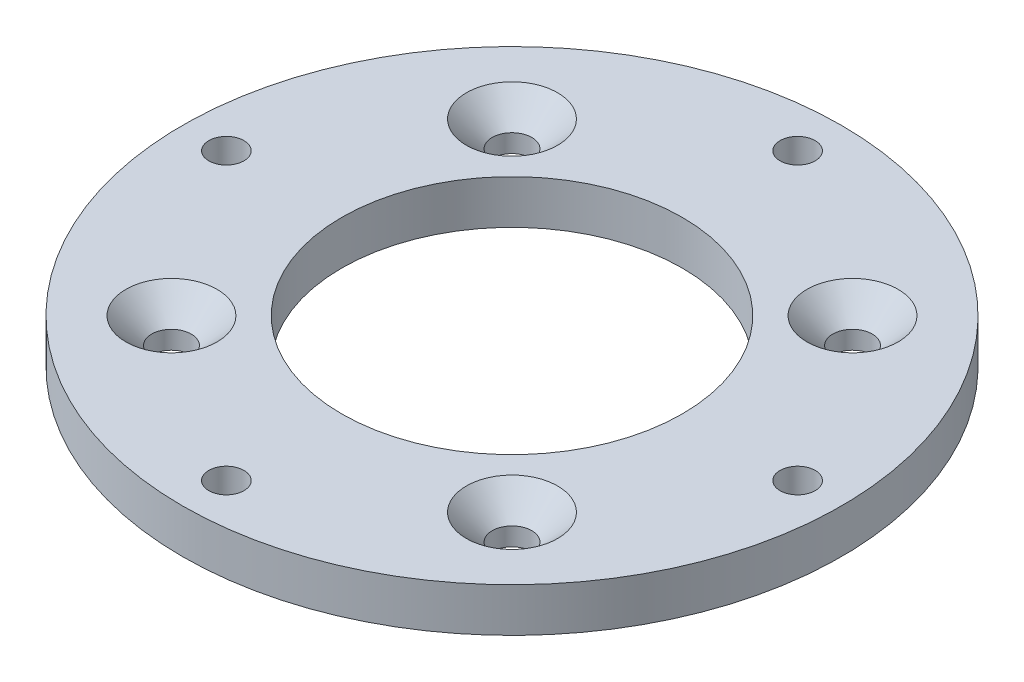
SolidWorks part; units mm, degrees
material "Acrylic (Medium-high impact)"
ref_plane "Front Plane" through (0, 0, 0) normal (0, 0, 1) x (1, 0, 0)
ref_plane "Top Plane" through (0, 0, 0) normal (0, 1, 0) x (1, 0, 0)
ref_plane "Right Plane" through (0, 0, 0) normal (1, 0, 0) x (0, 0, -1)
sketch "Sketch1" plane through (0, 0, 0) normal (0, 1, 0) x (1, 0, 0)
  circle A0 centre (0, 0) radius 30
  dimension "D1" = 60
extrude "Boss-Extrude1" add sketch "Sketch1" against normal blind 4
sketch "Sketch8" plane through (0, -4, 0) normal (0, -1, 0) x (1, 0, 0)
  line L1 (-15.5, -15.5) -> (15.5, -15.5) construction
  line L2 (-15.5, -15.5) -> (-15.5, 15.5) construction
  line L3 (-15.5, 15.5) -> (15.5, 15.5) construction
  line L4 (15.5, -15.5) -> (15.5, 15.5) construction
  line L5 (-15.5, -15.5) -> (15.5, 15.5) construction
  line L6 (-15.5, 15.5) -> (15.5, -15.5) construction
  circle A0 centre (0, 0) radius 15.5
  point P8 (0, 0)
  point P9 (0, 0)
  point P10 (0, 0)
  dimension "D1" = 31
extrude "Cut-Extrude1" cut sketch "Sketch8" against normal blind 6
sketch "Sketch14" plane through (0, 0, 0) normal (0, 1, 0) x (1, 0, 0)
  line L16 (-15.5, -15.5) -> (15.5, -15.5) construction
  line L17 (-15.5, -15.5) -> (-15.5, 15.5) construction
  line L18 (-15.5, 15.5) -> (15.5, 15.5) construction
  line L19 (15.5, -15.5) -> (15.5, 15.5) construction
  line L20 (-15.5, -15.5) -> (15.5, 15.5) construction
  line L21 (-15.5, 15.5) -> (15.5, -15.5) construction
  point P1889 (15.5, 15.5)
  point P1896 (-15.5, 15.5)
  point P1899 (-15.5, -15.5)
  point P1902 (15.5, -15.5)
  point P1903 (0, 0)
  dimension "D1" = 31
hole_wizard "CSK for M3 Countersunk Flat Head Screw2" positions "Sketch14" profile "Sketch16" countersink size "M3" standard "ISO" end condition through all
sketch "Sketch16" plane through (15.5, 0, 15.5) normal (1, 0, 0) x (0, 0, 1)
  line L0 (0, 0) -> (0, 4)
  line L1 (0, 4) -> (1.8, 4)
  line L2 (1.8, 4) -> (1.8, 2.35)
  line L3 (1.8, 2.35) -> (4.15, 0)
  line L5 (4.15, 0) -> (0, 0)
  line L6 (-1.8, 2.35) -> (-4.15, 0) construction
  line L11 (0, -6.35) -> (0, 107.95) construction
  dimension "Thru Hole Dia." = 3.6
  dimension "Thru Hole Depth" = 4
  dimension "Near C'Sink Dia." = 8.3
  dimension "Near C'Sink Angle" = 90
sketch "Sketch18" plane through (0, -4, 0) normal (0, -1, 0) x (1, 0, 0)
  point P0 (0, 26)
  point P5 (26, 0)
  point P6 (0, -26)
  point P7 (-26, 0)
  point P18 (0, 0)
  point P19 (0, 0)
  point P20 (0, 0)
  point P21 (0, 0)
  point P22 (0, 0)
  point P23 (0, 0)
  dimension "D1" = 26
  dimension "D2" = 4
hole_wizard "CSK for M3 Countersunk Flat Head Screw3" positions "Sketch18" profile "Sketch20" countersink size "M3" standard "ISO" end condition through all
sketch "Sketch20" plane through (0, -4, 26) normal (1, 0, 0) x (0, 0, -1)
  line L0 (0, 0) -> (0, 4)
  line L1 (0, 4) -> (1.6, 4)
  line L2 (1.6, 4) -> (1.6, 1.55)
  line L3 (1.6, 1.55) -> (3.15, 0)
  line L5 (3.15, 0) -> (0, 0)
  line L6 (-1.6, 1.55) -> (-3.15, 0) construction
  line L11 (0, -6.35) -> (0, 107.95) construction
  dimension "Thru Hole Dia." = 3.2
  dimension "Thru Hole Depth" = 4
  dimension "Near C'Sink Dia." = 6.3
  dimension "Near C'Sink Angle" = 90
